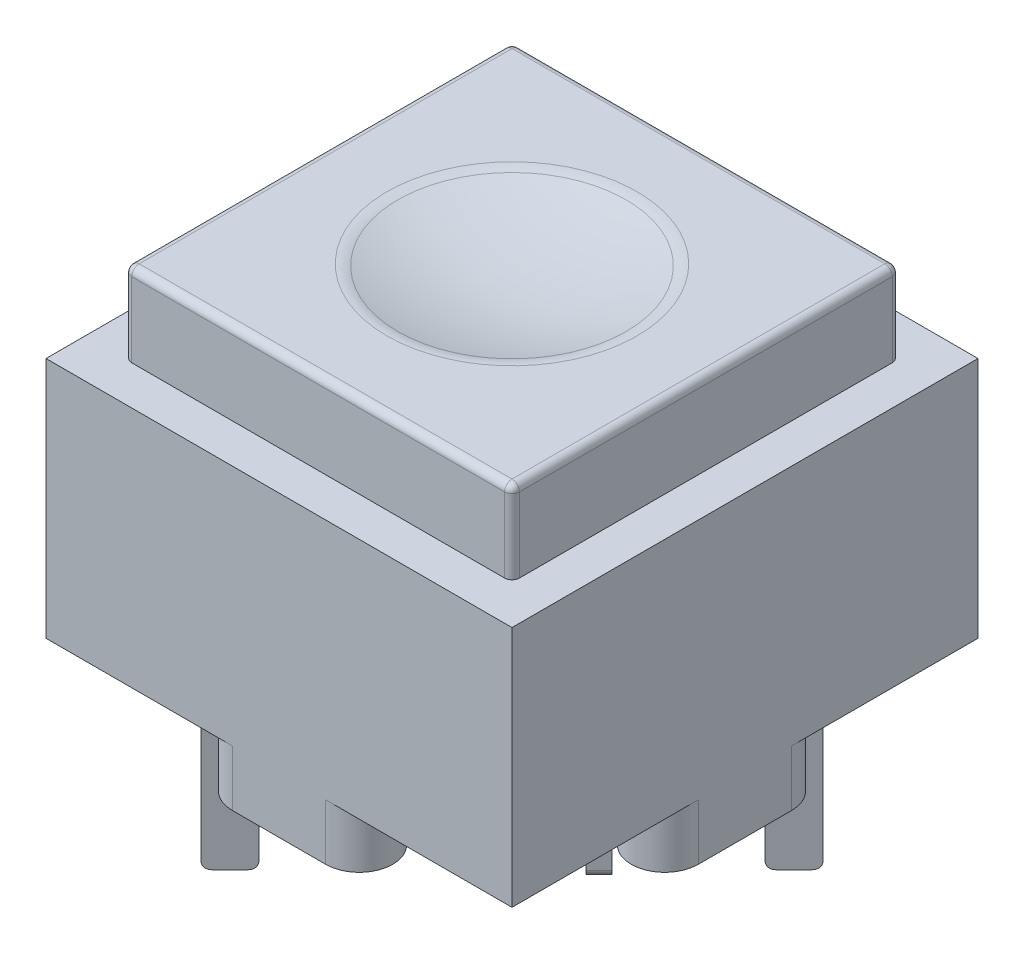
SolidWorks part; units mm, degrees
ref_plane "Спереди" through (0, 0, 0) normal (0, 0, 1) x (1, 0, 0)
ref_plane "Сверху" through (0, 0, 0) normal (0, 1, 0) x (1, 0, 0)
ref_plane "Справа" through (0, 0, 0) normal (1, 0, 0) x (0, 0, -1)
sketch "Эскиз1" plane through (0, 0, 0) normal (0, 1, 0) x (1, 0, 0)
  line L1 (-6.25, 6.25) -> (6.25, 6.25)
  line L2 (-6.25, 6.25) -> (-6.25, -6.25)
  line L3 (-6.25, -6.25) -> (6.25, -6.25)
  line L4 (6.25, 6.25) -> (6.25, -6.25)
  line L5 (-6.25, 6.25) -> (6.25, -6.25) construction
  line L6 (-6.25, -6.25) -> (6.25, 6.25) construction
  point P0 (0, 0)
  dimension "D1" = 12.5
extrude "Бобышка-Вытянуть1" add sketch "Эскиз1" along normal blind 6.5
sketch "Эскиз2" plane through (0, 0, 0) normal (0, -1, 0) x (1, 0, 0)
  line L0 (0, 0) -> (0, -5.35) construction
  line L1 (-6.25, 6.25) -> (6.25, 6.25) construction
  line L3 (6.25, 6.25) -> (-6.25, -6.25) construction
  line L4 (-1.2515, 5.35) -> (1.2515, 5.35) construction
  line L5 (-1.2515, 6.25) -> (1.2515, 6.25)
  line L6 (-1.2515, 4.45) -> (1.2515, 4.45)
  line L7 (5.35, -1.2515) -> (5.35, 1.2515) construction
  line L8 (6.25, -1.2515) -> (6.25, 1.2515)
  line L9 (4.45, -1.2515) -> (4.45, 1.2515)
  line L10 (-5.35, -1.2515) -> (-5.35, 1.2515) construction
  line L11 (-6.25, -1.2515) -> (-6.25, 1.2515)
  line L12 (-4.45, -1.2515) -> (-4.45, 1.2515)
  line L13 (-6.25, 0) -> (6.25, 0) construction
  line L15 (6.25, -6.25) -> (-6.25, -6.25) construction
  arc A0 (-1.2515, 6.25) -> (-1.2515, 4.45) centre (-1.2515, 5.35) ccw
  arc A1 (1.2515, 4.45) -> (1.2515, 6.25) centre (1.2515, 5.35) ccw
  arc A2 (6.25, -1.2515) -> (4.45, -1.2515) centre (5.35, -1.2515) cw
  arc A3 (4.45, 1.2515) -> (6.25, 1.2515) centre (5.35, 1.2515) cw
  arc A4 (-6.25, -1.2515) -> (-4.45, -1.2515) centre (-5.35, -1.2515) ccw
  arc A5 (-4.45, 1.2515) -> (-6.25, 1.2515) centre (-5.35, 1.2515) ccw
  circle A6 centre (0, -5.35) radius 0.85
  point P12 (0, 5.35)
  point P19 (5.35, 0)
  point P26 (-5.35, 0)
  dimension "D1" = 0.9
  dimension "D2" = 1.7
  dimension "D3" = 0.9
extrude "Бобышка-Вытянуть2" add sketch "Эскиз2" along normal blind 1.5
sketch "Эскиз5" plane through (0, 0, 0) normal (0, -1, 0) x (1, 0, 0)
  line L0 (-6.25, 6.25) -> (6.25, -6.25) construction
  line L1 (-3.783, 3.783) -> (3.783, -3.783) construction
  line L2 (-3.9952, 4.3487) -> (-3.2173, 3.5709)
  line L3 (-3.9952, 4.3487) -> (-4.3487, 3.9952)
  line L4 (-4.3487, 3.9952) -> (-3.5709, 3.2173)
  line L5 (-3.2173, 3.5709) -> (-3.5709, 3.2173)
  line L6 (-3.9952, 4.3487) -> (-3.5709, 3.2173) construction
  line L7 (-4.3487, 3.9952) -> (-3.2173, 3.5709) construction
  line L8 (0, 0) -> (6.25, 6.25) construction
  line L9 (3.9952, -4.3487) -> (3.2173, -3.5709)
  line L10 (3.5709, -3.2173) -> (3.2173, -3.5709)
  line L11 (4.3487, -3.9952) -> (3.5709, -3.2173)
  line L12 (4.3487, -3.9952) -> (3.9952, -4.3487)
  line L13 (3.783, -3.783) -> (1.1667, -1.1667) construction
  line L14 (0.601, -1.3789) -> (1.3789, -0.601)
  line L15 (0.601, -1.3789) -> (0.9546, -1.7324)
  line L16 (0.9546, -1.7324) -> (1.7324, -0.9546)
  line L17 (1.3789, -0.601) -> (1.7324, -0.9546)
  line L18 (1.3789, -0.601) -> (0.9546, -1.7324) construction
  point P4 (-3.783, 3.783)
  dimension "D1" = 0.5
  dimension "D2" = 1.1
  dimension "D3" = 10.7
  dimension "D4" = 3.7
  dimension "D5" = 1.1
  dimension "D6" = 0.5
extrude "Бобышка-Вытянуть3" add sketch "Эскиз5" along normal blind 5.2 separate body
fillet "Скругление2" radius 0.2 2 edges at (-4.1719, -5.2, 4.1719) (-3.3941, -5.2, 3.3941)
fillet "Скругление3" radius 0.2 2 edges at (1.5556, -5.2, -0.7778) (0.7778, -5.2, -1.5556)
fillet "Скругление4" radius 0.2 2 edges at (3.3941, -5.2, -3.3941) (4.1719, -5.2, -4.1719)
sketch "Эскиз6" plane through (0, 6.5, 0) normal (0, 1, 0) x (1, 0, 0)
  line L1 (-5.2, 5.2) -> (5.2, 5.2)
  line L2 (-5.2, 5.2) -> (-5.2, -5.2)
  line L3 (-5.2, -5.2) -> (5.2, -5.2)
  line L4 (5.2, 5.2) -> (5.2, -5.2)
  line L5 (-5.2, 5.2) -> (5.2, -5.2) construction
  line L6 (-5.2, -5.2) -> (5.2, 5.2) construction
  point P0 (0, 0)
  dimension "D1" = 10.4
extrude "Бобышка-Вытянуть4" add sketch "Эскиз6" along normal blind 2.2 separate body
fillet "Скругление5" radius 0.2 8 edges at (5.2, 7.6, -5.2) (5.2, 7.6, 5.2) (-5.2, 7.6, 5.2) (-5.2, 7.6, -5.2) (0, 8.7, 5.2) (5.2, 8.7, 0) (0, 8.7, -5.2) (-5.2, 8.7, 0)
sketch "Эскиз7" plane through (0, 0, 0) normal (0, 0, 1) x (1, 0, 0)
  line L0 (-5, 8.7) -> (5, 8.7) construction
  line L2 (5.2, 8.5) -> (5.2, 6.5) construction
  line L3 (0, 8.7) -> (3.2, 8.7)
  line L4 (0, 8.2) -> (0, 8.7)
  arc A0 (0, 8.2) -> (3.2, 8.7) centre (0, 18.69) ccw
  point P9 (0, 8.2)
  dimension "D4" = 10.49
  dimension "D1" = 3.2
  dimension "D2" = 2
  dimension "D3" = 0.5
revolve "Вырез-Повернуть1" cut sketch "Эскиз7" angle 360 about L4
fillet "Скругление6" radius 1 1 edges at (3.2, 8.7, 0)
